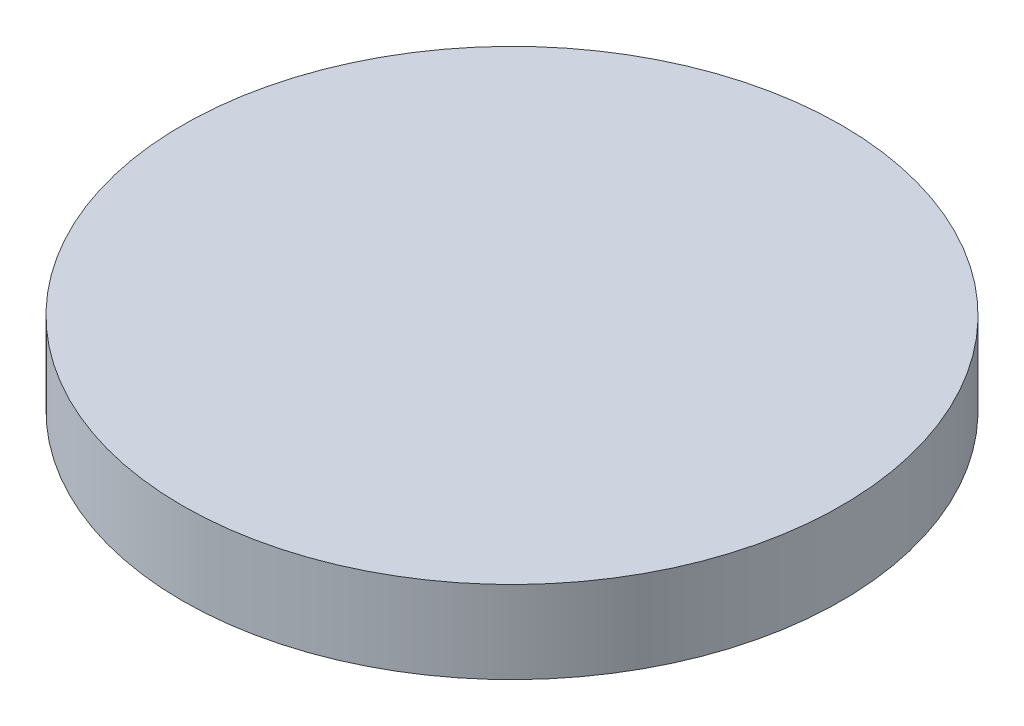
SolidWorks part; units mm, degrees
ref_plane "Front Plane" through (0, 0, 0) normal (0, 0, 1) x (1, 0, 0)
ref_plane "Top Plane" through (0, 0, 0) normal (0, 1, 0) x (1, 0, 0)
ref_plane "Right Plane" through (0, 0, 0) normal (1, 0, 0) x (0, 0, -1)
sketch "Sketch2" plane through (0, 0, 0) normal (0, 1, 0) x (1, 0, 0)
  line L0 (0, 0) -> (0, 13.1466) construction
  line L1 (0, 0) -> (7.3499, 0) construction
  circle A1 centre (0, 0) radius 40
  dimension "D2" = 80
extrude "Boss-Extrude1" add sketch "Sketch2" along normal blind 10
sketch "Sketch3" plane through (0, 10, 0) normal (0, 1, 0) x (1, 0, 0)
  line L0 (0, 0) -> (0, 10.6101) construction
  line L1 (0, 0) -> (8.7575, 0) construction
  circle A1 centre (0, 34) radius 1.6
  circle A2 centre (29.4449, 17) radius 1.6
  circle A3 centre (29.4449, -17) radius 1.6
  circle A4 centre (0, -34) radius 1.6
  circle A5 centre (-29.4449, -17) radius 1.6
  circle A6 centre (-29.4449, 17) radius 1.6
  circle A7 centre (0, 34) radius 3
  circle A8 centre (29.4449, 17) radius 3
  circle A9 centre (29.4449, -17) radius 3
  circle A10 centre (0, -34) radius 3
  circle A11 centre (-29.4449, -17) radius 3
  circle A12 centre (-29.4449, 17) radius 3
  point P22 (0, 0)
  point P31 (0, 0)
  dimension "D1" = 6
  dimension "D2" = 3.2
  dimension "D3" = 6
  dimension "D4" = 6
